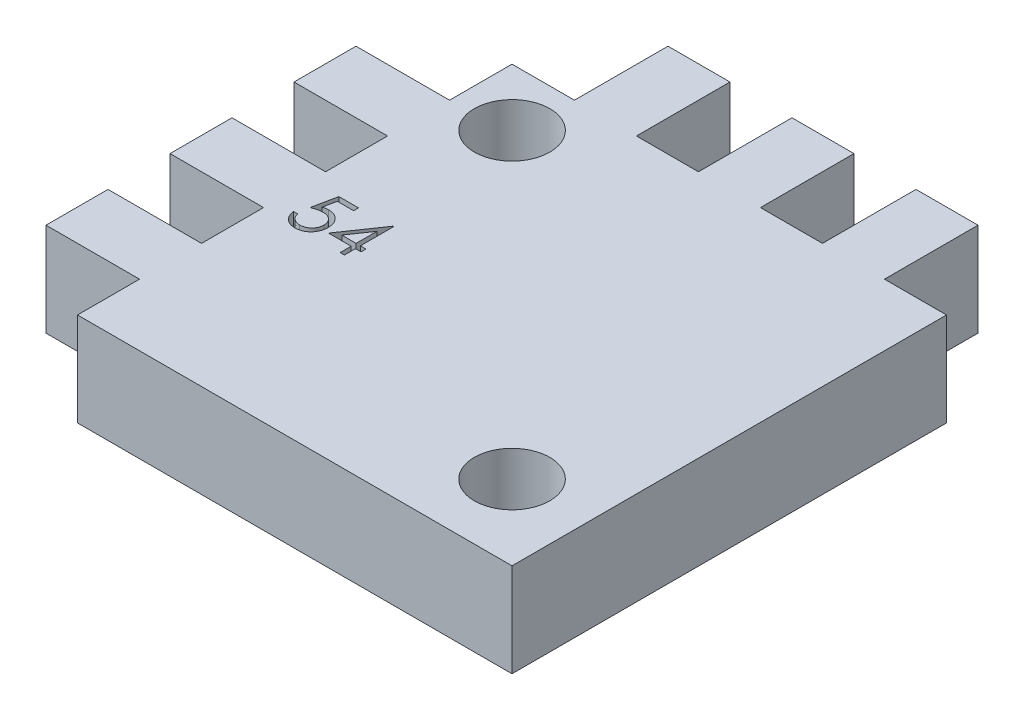
SolidWorks part; units mm, degrees
material "Acrylic (Medium-high impact)"
ref_plane "Front Plane" through (0, 0, 0) normal (0, 0, 1) x (1, 0, 0)
ref_plane "Top Plane" through (0, 0, 0) normal (0, 1, 0) x (1, 0, 0)
ref_plane "Right Plane" through (0, 0, 0) normal (1, 0, 0) x (0, 0, -1)
sketch "Sketch1" plane through (0, 0, 0) normal (0, 1, 0) x (1, 0, 0)
  line L2 (0, 24.66) -> (0, 20.55)
  line L4 (35, 28.8) -> (35, 18)
  line L6 (0, 16.44) -> (0, 12.33)
  line L7 (6.2, 0) -> (17, 0)
  line L9 (26.301, 0) -> (6.2, 0) construction
  line L11 (0, 24.66) -> (0, 20.55) construction
  line L12 (26.78, 35) -> (30.89, 35)
  line L13 (0, 4.11) -> (6.2, 4.11)
  line L16 (6.2, 4.11) -> (6.2, 0)
  line L17 (0, 12.33) -> (6.2, 12.33)
  line L19 (0, 8.22) -> (6.2, 8.22)
  line L20 (6.2, 12.33) -> (6.2, 8.22)
  line L21 (0, 20.55) -> (6.2, 20.55)
  line L23 (0, 16.44) -> (6.2, 16.44)
  line L24 (6.2, 20.55) -> (6.2, 16.44)
  line L25 (35, 28.8) -> (30.89, 28.8)
  line L28 (30.89, 28.8) -> (30.89, 35)
  line L30 (22.67, 35) -> (22.67, 28.8)
  line L31 (22.67, 28.8) -> (26.78, 28.8)
  line L32 (26.78, 35) -> (26.78, 28.8)
  line L34 (14.45, 35) -> (14.45, 28.8)
  line L35 (14.45, 28.8) -> (18.56, 28.8)
  line L36 (18.56, 35) -> (18.56, 28.8)
  line L39 (0, 24.66) -> (6.2, 24.66)
  line L40 (6.2, 28.8) -> (6.2, 24.66)
  line L43 (6.2, 28.8) -> (10.34, 28.8)
  line L44 (10.34, 35) -> (10.34, 28.8)
  line L45 (18.56, 35) -> (22.67, 35)
  line L46 (10.34, 35) -> (14.45, 35)
  line L47 (0, 20.55) -> (0, 24.66) construction
  line L48 (0, 16.44) -> (0, 12.33) construction
  line L49 (0, 12.33) -> (0, 16.44) construction
  line L50 (0, 8.22) -> (0, 4.11)
  line L51 (0, 8.22) -> (0, 4.11) construction
  line L52 (0, 4.11) -> (0, 8.22) construction
  line L54 (6.2, 0) -> (62.7069, 0) construction
  line L55 (17, 0) -> (35, 0)
  line L56 (35, 18) -> (35, 0)
  circle A0 centre (10.006, 25) radius 2.5
  circle A2 centre (30.0224, 4.9806) radius 2.5
  dimension "D5" = 5
  dimension "D4" = 5
  dimension "D8" = 6.2
  dimension "D9" = 6.2
  dimension "D13" = 4.11
  dimension "D14" = 6.2
  dimension "D15" = 6.2
  dimension "D16" = 6.2
  dimension "D17" = 6.2
  dimension "D21" = 4.11
  dimension "D22" = 4.11
  dimension "D23" = 4.11
  dimension "D24" = 4.11
  dimension "D25" = 4.11
  dimension "D26" = 4.11
  dimension "D27" = 4.11
  dimension "D28" = 4.11
  dimension "D29" = 4.11
  dimension "D30" = 4.11
  dimension "D31" = 6.2
  dimension "D32" = 6.2
  dimension "D33" = 4.11
extrude "Boss-Extrude1" add sketch "Sketch1" along normal blind 6.2
sketch "Sketch2" plane through (0, 6.2, 0) normal (0, 1, 0) x (1, 0, 0)
  line L0 (-13.4604, 16.6244) -> (25.6719, 16.6244) construction
  text T0 "54"
extrude "Cut-Extrude1" cut sketch "Sketch2" against normal blind 1
